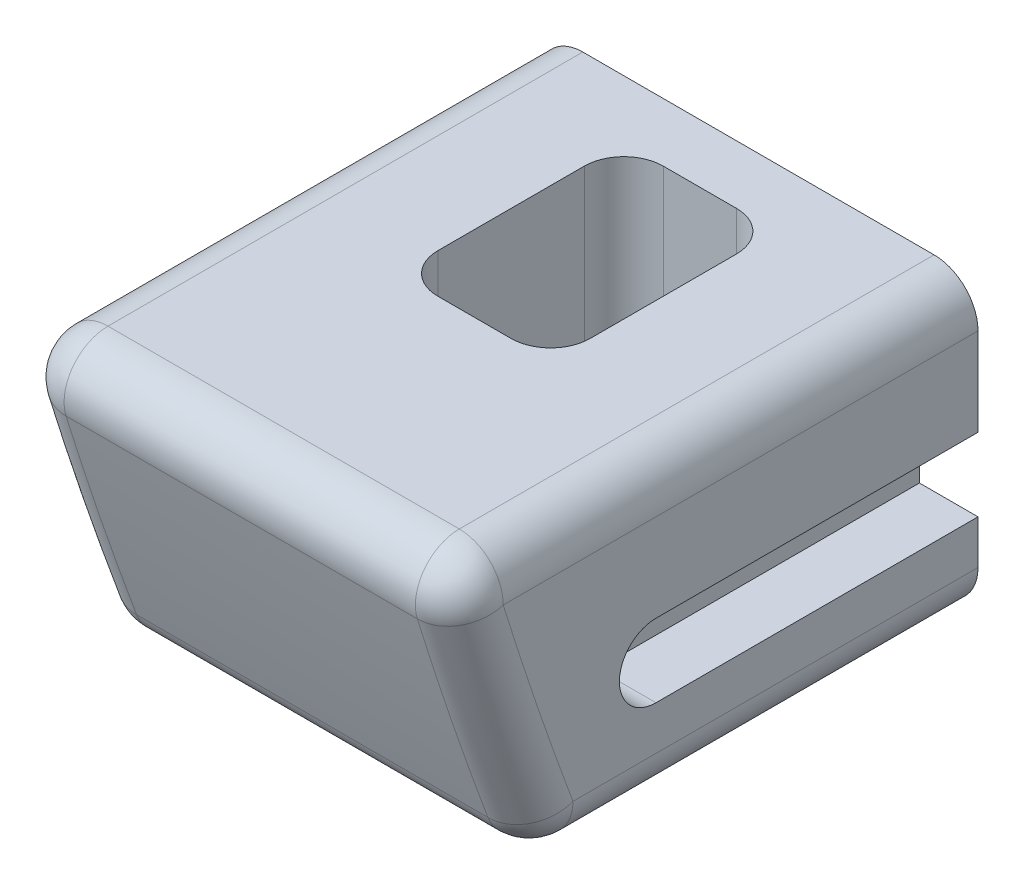
SolidWorks part; units mm, degrees
ref_plane "Front plane" through (0, 0, 0) normal (0, 0, 1) x (1, 0, 0)
ref_plane "Top plane" through (0, 0, 0) normal (0, 1, 0) x (1, 0, 0)
ref_plane "Right Plane" through (0, 0, 0) normal (1, 0, 0) x (0, 0, -1)
sketch "Sketch1" plane through (0, 0, 0) normal (0, 0, 1) x (1, 0, 0)
  line L1 (7.5, 0) -> (-7.5, 0)
  line L2 (7.5, 0) -> (7.5, 8)
  line L3 (7.5, 8) -> (-7.5, 8)
  line L4 (-7.5, 0) -> (-7.5, 8)
  point P4 (0, 0)
  dimension "D1" = 15
  dimension "D2" = 8
extrude "Boss-Extrude1" add sketch "Sketch1" along normal blind 10
sketch "Sketch2" plane through (0, 8, 0) normal (0, 1, 0) x (1, 0, 0)
  line L0 (-1.25, -2) -> (1.25, -2)
  line L1 (2.6, -3.35) -> (2.6, -8.35)
  line L2 (1.25, -9.7) -> (-1.25, -9.7)
  line L3 (-2.6, -8.35) -> (-2.6, -3.35)
  line L4 (7.5, 0) -> (-7.5, 0) construction
  arc A0 (1.25, -2) -> (2.6, -3.35) centre (1.25, -3.35) cw
  arc A1 (2.6, -8.35) -> (1.25, -9.7) centre (1.25, -8.35) cw
  arc A2 (-1.25, -9.7) -> (-2.6, -8.35) centre (-1.25, -8.35) cw
  arc A3 (-2.6, -3.35) -> (-1.25, -2) centre (-1.25, -3.35) cw
  point P12 (0, -2)
  dimension "D2" = 2.5
  dimension "D1" = 2
  dimension "D3" = 5
  dimension "D4" = 1.35
extrude "Cut-Extrude1" cut sketch "Sketch2" against normal through all
sketch "Sketch3" plane through (-7.5, 0, 0) normal (1, 0, 0) x (0, 0, -1)
  line L2 (-14.8733, -2) -> (0, -2)
  line L3 (0, -2) -> (0, 0)
  line L4 (-14.6479, 6.5) -> (-16.2187, 6.5)
  line L5 (1.25, 8) -> (-15.1071, 8)
  line L6 (0, 3.4) -> (0, 4.9638)
  line L7 (-14.3842, 1) -> (-10, 1)
  line L12 (0, 0) -> (-10, 0)
  line L37 (-10, 3.4) -> (0, 3.4)
  line L38 (-10, 8) -> (-10, 0) construction
  line L39 (-10, 1) -> (-10, 3.4)
  line L45 (4.2862, 4.9638) -> (1.25, 8)
  line L46 (4.2862, 4.9638) -> (1.25, 8)
  line L47 (0, 4.9638) -> (4.2862, 4.9638)
  line L48 (-10, 8) -> (-10, 0)
  line L50 (-10, 8) -> (-18.2355, 8)
  line L51 (0, 4.9638) -> (4.2862, 4.9638)
  line L83 (-10, 8) -> (0, 8) construction
  arc A1 (-16.2187, 6.5) -> (-14.3842, 1) centre (107.62, 44.75) ccw
  arc A2 (-16.6721, 8) -> (-13.2664, -2) centre (107.62, 44.75) ccw construction
  arc A3 (-18.2355, 8) -> (-14.8733, -2) centre (107.62, 44.75) ccw
  arc A4 (-17.8837, 6.816) -> (-14.2694, -3.5526) centre (107.62, 44.75) ccw construction
  arc A5 (-16.4479, 7.25) -> (-12.8749, -3) centre (107.62, 44.75) ccw construction
  arc A9 (-15.1071, 8) -> (-14.6479, 6.5) centre (107.62, 44.75) ccw
  dimension "D2" = 2
  dimension "D1" = 0
  dimension "D3" = 1.5
extrude "Boss-Extrude2" add sketch "Sketch3" along normal up to vertex (15 mm away) up to point (7.5, 0, 10)
sketch "Sketch7" plane through (0, 8, 0) normal (0, 1, 0) x (1, 0, 0)
  line L0 (-2.6, -11.2355) -> (-7.5, -11.2355)
  line L4 (-2.6, -3.35) -> (-2.6, -8.35)
  line L5 (1.25, -2) -> (-1.25, -2)
  line L6 (2.6, -8.35) -> (2.6, -3.35)
  line L7 (-1.25, -9.7) -> (1.25, -9.7)
  line L8 (-2.6, -11.2355) -> (-2.6, -8.35)
  line L10 (2.6, -8.35) -> (2.6, -11.2355)
  line L11 (-1.25, -9.7) -> (1.25, -9.7)
  line L12 (7.5, 0) -> (-7.5, 0)
  line L13 (-7.5, 0) -> (-7.5, -18.2355)
  line L14 (-7.5, -18.2355) -> (7.5, -18.2355)
  line L15 (7.5, -18.2355) -> (7.5, 0)
  line L16 (7.5, -11.2355) -> (2.6, -11.2355)
  line L17 (-7.5, -11.2355) -> (-7.5, -18.2355)
  line L19 (7.5, -18.2355) -> (7.5, -11.2355)
  line L22 (-7.5, -18.2355) -> (7.5, -18.2355)
  arc A4 (-1.25, -2) -> (-2.6, -3.35) centre (-1.25, -3.35) ccw
  arc A5 (2.6, -3.35) -> (1.25, -2) centre (1.25, -3.35) ccw
  arc A6 (1.25, -9.7) -> (2.6, -8.35) centre (1.25, -8.35) ccw
  arc A7 (-2.6, -8.35) -> (-1.25, -9.7) centre (-1.25, -8.35) ccw
  arc A10 (1.25, -9.7) -> (2.6, -8.35) centre (1.25, -8.35) ccw
  arc A11 (-2.6, -8.35) -> (-1.25, -9.7) centre (-1.25, -8.35) ccw
  dimension "D1" = 0
  dimension "D2" = 0
extrude "Boss-Extrude3" [suppressed] add sketch "Sketch7" along normal blind 15
draft "Draft1" [suppressed] type of draft neutral plane draft angle 15 faces to draft 2 parameters "D1"=15
fillet "Fillet2" [suppressed] radius 0.5
sketch "Sketch5" plane through (7.5, 0, 0) normal (1, 0, 0) x (0, 0, -1)
  line L0 (0, 1) -> (-11, 1)
  line L1 (0, -2) -> (0, 8) construction
  line L2 (-11, 3.5) -> (0, 3.5)
  line L3 (0, 3.5) -> (0, 1)
  line L5 (-18.2355, 8) -> (0, 8) construction
  arc A0 (-11, 1) -> (-11, 3.5) centre (-11, 2.25) cw
  dimension "D1" = 2.5
  dimension "D2" = 7
  dimension "D3" = 11
extrude "Cut-Extrude2" cut sketch "Sketch5" against normal blind 2
mirror "Mirror1" about plane through (0, 0, 0) normal (1, 0, 0) of "Cut-Extrude2"
sketch "Sketch6" plane through (0, 0, 0) normal (0, 1, 0) x (1, 0, 0)
  circle A0 centre (-1.25, -3.35) radius 0.8
  circle A2 centre (1.25, -3.35) radius 0.8
  circle A3 centre (1.25, -5.85) radius 0.8
  circle A4 centre (1.25, -8.35) radius 0.8
  circle A5 centre (-1.25, -5.85) radius 0.8
  circle A6 centre (-1.25, -8.35) radius 0.8
  arc A9 (1.25, -9.7) -> (2.6, -8.35) centre (1.25, -8.35) ccw construction
  dimension "D3" = 1.6
  dimension "D1" = 2
  dimension "D2" = 3
extrude "Cut-Extrude3" cut sketch "Sketch6" against normal through all both and the other way through all
fillet "Fillet1" radius 1.5 8 edges at (-7.5, 8, 9.1177) (7.5, 8, 9.1177) (-7.5, -2, 7.4366) (7.5, -2, 7.4366) (0, -2, 14.8733) (-7.5, 2.9662, 16.655) (7.5, 2.9662, 16.655) (0, 8, 18.2355)
